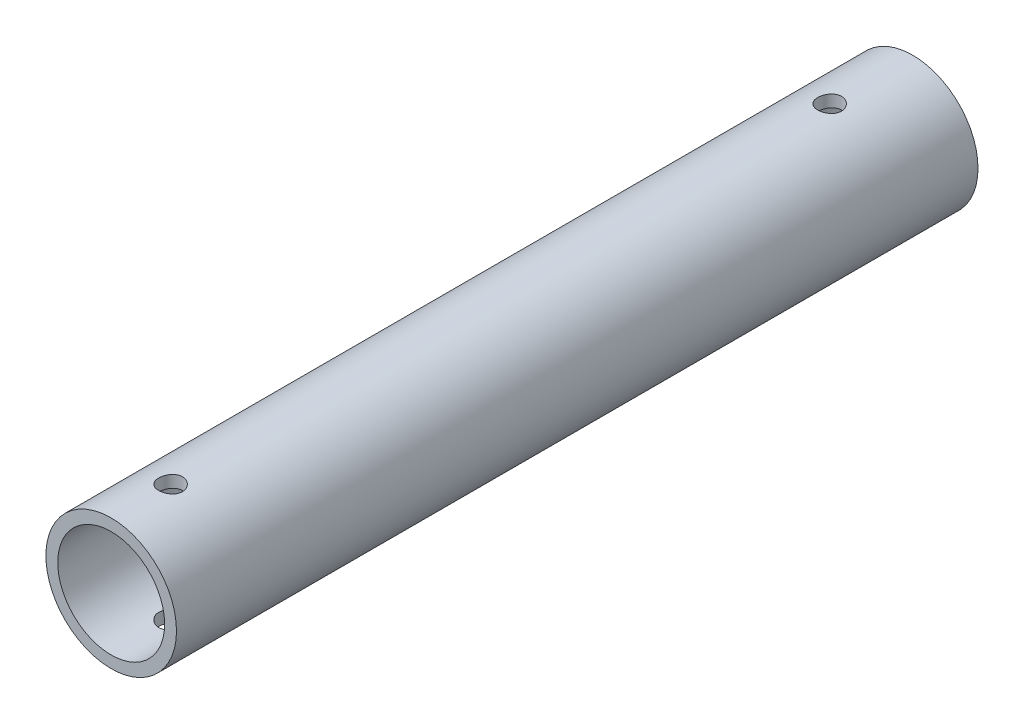
SolidWorks part; units mm, degrees
ref_plane "Ön Düzlem" through (0, 0, 0) normal (0, 0, 1) x (1, 0, 0)
ref_plane "Üst Düzlem" through (0, 0, 0) normal (0, 1, 0) x (1, 0, 0)
ref_plane "Sağ Düzlem" through (0, 0, 0) normal (1, 0, 0) x (0, 0, -1)
sketch "Sketch1" plane through (0, 0, 0) normal (0, 0, 1) x (1, 0, 0)
  circle A0 centre (0, 0) radius 5.5
  circle A1 centre (0, 0) radius 4.5
  dimension "D1" = 9
  dimension "D2" = 1
extrude "Boss-Extrude1" add sketch "Sketch1" along normal blind 67.5
sketch "Çizim2" plane through (0, 0, 0) normal (0, 1, 0) x (1, 0, 0)
  circle A0 centre (0, -7) radius 1
  dimension "D2" = 2
  dimension "D1" = 7
extrude "Kes-Ekstrüzyon1" cut sketch "Çizim2" against normal through all both and the other way through all
sketch "Çizim3" plane through (0, 0, 0) normal (0, 1, 0) x (1, 0, 0)
  line L0 (-5.5, -67.5) -> (5.5, -67.5) construction
  circle A0 centre (0, -62.5) radius 1
  dimension "D2" = 2
  dimension "D1" = 5
extrude "Kes-Ekstrüzyon2" cut sketch "Çizim3" against normal through all both and the other way through all
